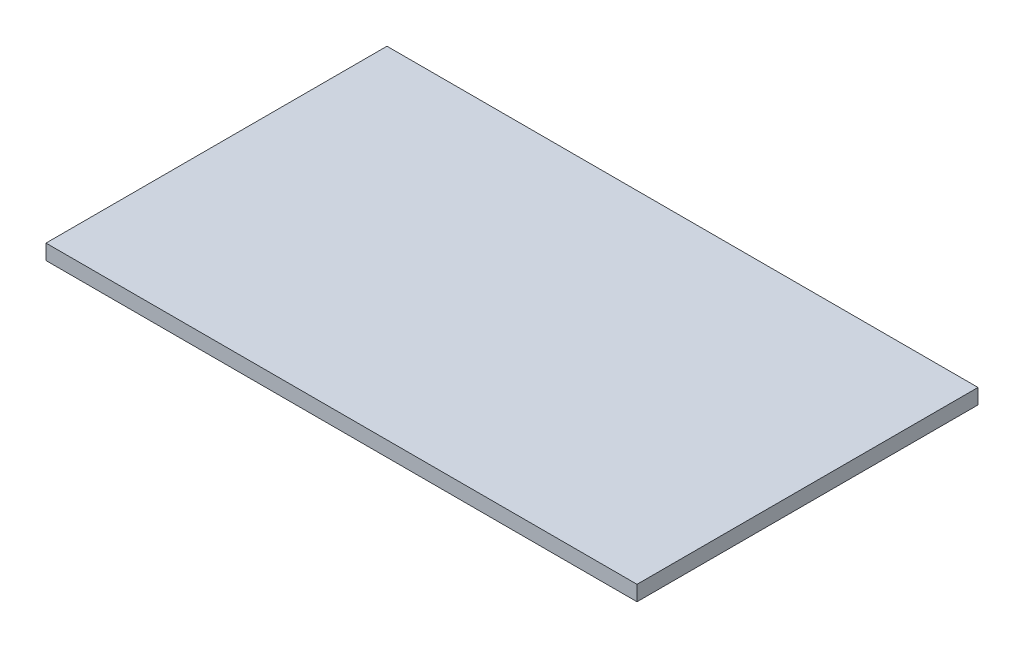
SolidWorks part; units mm, degrees
ref_plane "Alzado" through (0, 0, 0) normal (0, 0, 1) x (1, 0, 0)
ref_plane "Planta" through (0, 0, 0) normal (0, 1, 0) x (1, 0, 0)
ref_plane "Vista lateral" through (0, 0, 0) normal (1, 0, 0) x (0, 0, -1)
sketch "Croquis1" plane through (0, 0, 0) normal (0, 1, 0) x (1, 0, 0)
  line L1 (390, -225) -> (-390, -225)
  line L2 (390, -225) -> (390, 225)
  line L3 (390, 225) -> (-390, 225)
  line L4 (-390, -225) -> (-390, 225)
  line L5 (390, -225) -> (-390, 225) construction
  line L6 (390, 225) -> (-390, -225) construction
  point P0 (0, 0)
  dimension "D1" = 780
  dimension "D2" = 450
extrude "Saliente-Extruir1" add sketch "Croquis1" along normal blind 20
sketch "Croquis2" plane through (0, 20, 0) normal (0, 1, 0) x (1, 0, 0)
  line L0 (-250, 225) -> (-250, -225) construction
  line L1 (390, 225) -> (-390, 225) construction
  line L2 (-390, -225) -> (390, -225) construction
  line L3 (250, 225) -> (250, -225) construction
  line L4 (-250, 0) -> (250, 0) construction
  point P13 (0, 0)
  dimension "D1" = 500
sketch "Croquis3" plane through (0, 20, 0) normal (0, 1, 0) x (1, 0, 0)
  line L0 (-390, 225) -> (-390, -225) construction
  line L1 (390, -225) -> (390, 225) construction
  line L2 (-390, -225) -> (390, -225) construction
  line L3 (-350, -115) -> (-150, -115) construction
  line L4 (150, -115) -> (350, -115) construction
  line L5 (-250, -115) -> (-293, -189.4782) construction
  line L6 (-250, -115) -> (-207, -189.4782) construction
  line L7 (250, -115) -> (207, -189.4782) construction
  line L8 (250, -115) -> (293, -189.4782) construction
  line L9 (-390, 225) -> (390, -225) construction
  line L10 (20, -74.4) -> (-20, -74.4) construction
  line L11 (20, -74.4) -> (20, -24.4) construction
  line L12 (20, -24.4) -> (-20, -24.4) construction
  line L13 (-20, -74.4) -> (-20, -24.4) construction
  line L14 (20, -74.4) -> (-20, -24.4) construction
  line L15 (20, -24.4) -> (-20, -74.4) construction
  line L16 (390, 225) -> (-390, -225) construction
  circle A0 centre (-293, -189.4782) radius 3
  circle A1 centre (-207, -189.4782) radius 3
  circle A2 centre (-336, -115) radius 3
  circle A3 centre (-164, -115) radius 3
  circle A4 centre (-20, -24.4) radius 3
  circle A5 centre (20, -24.4) radius 3
  circle A6 centre (-20, -74.4) radius 3
  circle A7 centre (20, -74.4) radius 3
  circle A8 centre (207, -189.4782) radius 3
  circle A9 centre (293, -189.4782) radius 3
  circle A10 centre (164, -115) radius 3
  circle A11 centre (336, -115) radius 3
  circle A12 centre (-250, -115) radius 100 construction
  circle A13 centre (250, -115) radius 100 construction
  circle A14 centre (0, -49.4) radius 40 construction
  circle A15 centre (-250, -115) radius 86 construction
  circle A16 centre (250, -115) radius 86 construction
  dimension "D1" = 200
  dimension "D2" = 80
  dimension "D6" = 172
  dimension "D8" = 6
  dimension "D10" = 175.6
  dimension "D11" = 390
  dimension "D3" = 140
  dimension "D4" = 140
  dimension "D5" = 110
  dimension "D7" = 60
  dimension "D9" = 60
  dimension "D12" = 40
  dimension "D13" = 50
